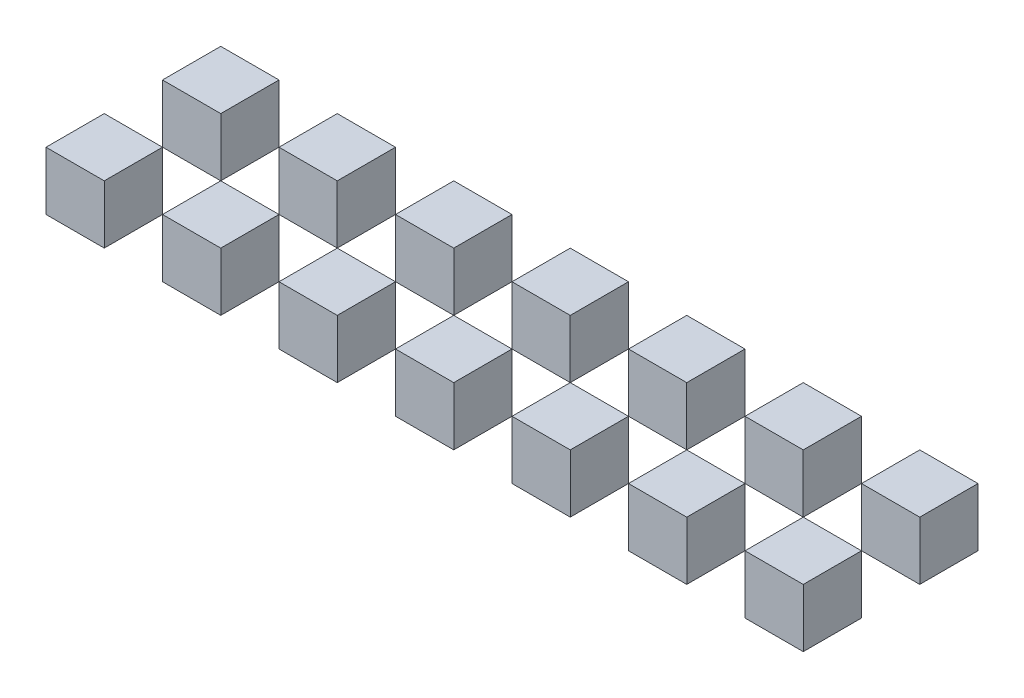
SolidWorks part; units mm, degrees
material "P-2 (Compression Quartz)"
ref_plane "Front Plane" through (0, 0, 0) normal (0, 0, 1) x (1, 0, 0)
ref_plane "Top Plane" through (0, 0, 0) normal (0, 1, 0) x (1, 0, 0)
ref_plane "Right Plane" through (0, 0, 0) normal (1, 0, 0) x (0, 0, -1)
sketch "Sketch1" plane through (0, 0, 0) normal (0, 1, 0) x (1, 0, 0)
  line L0 (50.8, 0) -> (25.4, 0)
  line L1 (0, 0) -> (-25.4, 0)
  line L2 (0, 0) -> (0, 25.4)
  line L3 (0, 25.4) -> (-25.4, 25.4)
  line L4 (-25.4, 0) -> (-25.4, 25.4)
  line L5 (50.8, 0) -> (50.8, 25.4)
  line L6 (50.8, 25.4) -> (25.4, 25.4)
  line L7 (25.4, 0) -> (25.4, 25.4)
  line L8 (101.6, 0) -> (76.2, 0)
  line L9 (101.6, 0) -> (101.6, 25.4)
  line L10 (101.6, 25.4) -> (76.2, 25.4)
  line L11 (76.2, 0) -> (76.2, 25.4)
  line L12 (152.4, 0) -> (127, 0)
  line L13 (152.4, 0) -> (152.4, 25.4)
  line L14 (152.4, 25.4) -> (127, 25.4)
  line L15 (127, 0) -> (127, 25.4)
  line L16 (203.2, 0) -> (177.8, 0)
  line L17 (203.2, 0) -> (203.2, 25.4)
  line L18 (203.2, 25.4) -> (177.8, 25.4)
  line L19 (177.8, 0) -> (177.8, 25.4)
  line L20 (254, 0) -> (228.6, 0)
  line L21 (254, 0) -> (254, 25.4)
  line L22 (254, 25.4) -> (228.6, 25.4)
  line L23 (228.6, 0) -> (228.6, 25.4)
  line L24 (304.8, 0) -> (279.4, 0)
  line L25 (304.8, 0) -> (304.8, 25.4)
  line L26 (304.8, 25.4) -> (279.4, 25.4)
  line L27 (279.4, 0) -> (279.4, 25.4)
  line L40 (50.8, 50.8) -> (25.4, 50.8)
  line L41 (50.8, 50.8) -> (50.8, 76.2)
  line L42 (50.8, 76.2) -> (25.4, 76.2)
  line L43 (25.4, 50.8) -> (25.4, 76.2)
  line L44 (101.6, 50.8) -> (76.2, 50.8)
  line L45 (101.6, 50.8) -> (101.6, 76.2)
  line L46 (101.6, 76.2) -> (76.2, 76.2)
  line L47 (76.2, 50.8) -> (76.2, 76.2)
  line L48 (152.4, 50.8) -> (127, 50.8)
  line L49 (152.4, 50.8) -> (152.4, 76.2)
  line L50 (152.4, 76.2) -> (127, 76.2)
  line L51 (127, 50.8) -> (127, 76.2)
  line L52 (203.2, 50.8) -> (177.8, 50.8)
  line L53 (203.2, 50.8) -> (203.2, 76.2)
  line L54 (203.2, 76.2) -> (177.8, 76.2)
  line L55 (177.8, 50.8) -> (177.8, 76.2)
  line L56 (254, 50.8) -> (228.6, 50.8)
  line L57 (254, 50.8) -> (254, 76.2)
  line L58 (254, 76.2) -> (228.6, 76.2)
  line L59 (228.6, 50.8) -> (228.6, 76.2)
  line L60 (304.8, 50.8) -> (279.4, 50.8)
  line L61 (304.8, 50.8) -> (304.8, 76.2)
  line L62 (304.8, 76.2) -> (279.4, 76.2)
  line L63 (279.4, 50.8) -> (279.4, 76.2)
  line L76 (0, 50.8) -> (-25.4, 50.8)
  line L77 (0, 50.8) -> (0, 76.2)
  line L78 (0, 76.2) -> (-25.4, 76.2)
  line L79 (-25.4, 50.8) -> (-25.4, 76.2)
  line L80 (0, 0) -> (50.8, 0) construction
  line L81 (0, 0) -> (0, 50.8) construction
  dimension "D1" = 25.4
  dimension "D4" = 50.8
  dimension "D5" = 50.8
  dimension "D2" = 7
  dimension "D3" = 2
extrude "Boss-Extrude1" add sketch "Sketch1" along normal blind 25.4
equation "\"D1@Boss-Extrude1\"=\"D1@Sketch1\""
equation "\"D5@Sketch1\"=2*\"D1@Sketch1\""
equation "\"D4@Sketch1\"=\"D5@Sketch1\""
